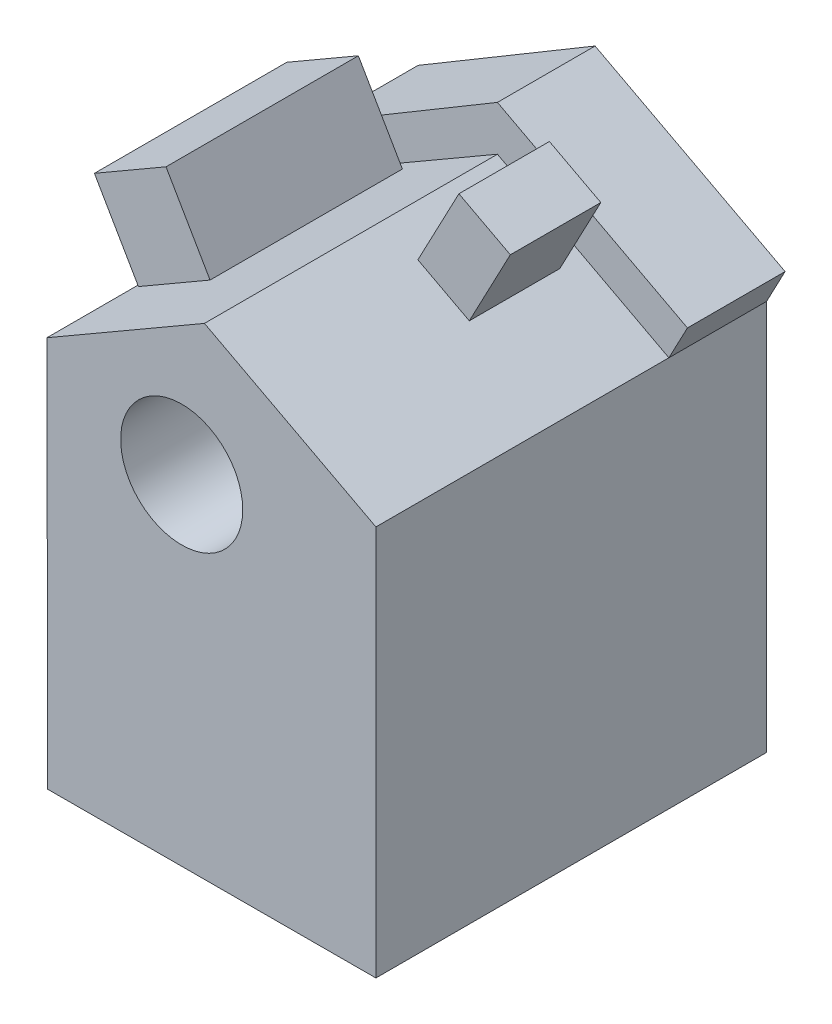
SolidWorks part; units mm, degrees
ref_plane "Front Plane" through (0, 0, 0) normal (0, 0, 1) x (1, 0, 0)
ref_plane "Top Plane" through (0, 0, 0) normal (0, 1, 0) x (1, 0, 0)
ref_plane "Right Plane" through (0, 0, 0) normal (1, 0, 0) x (0, 0, -1)
sketch "Sketch4" plane through (0, 0, 0) normal (0, 0, 1) x (1, 0, 0)
  line L0 (0, 0) -> (33.61, 0.0671)
  line L1 (0, 0) -> (-0.0798, 40)
  line L2 (-0.0798, 40) -> (16.0514, 49.3374)
  line L3 (16.0514, 49.3374) -> (33.61, 40.0671)
  line L4 (33.61, 40.0671) -> (33.61, 0.0671)
  dimension "D1" = 33.61
  dimension "D2" = 40
  dimension "D3" = 40
extrude "Boss-Extrude1" add sketch "Sketch4" along normal blind 40
sketch "Sketch5" plane through (0, 0, 40) normal (0, 0, 1) x (1, 0, 0)
  line L0 (0, 0) -> (33.61, 0.0671) construction
  line L6 (1.3588, 15.0227) -> (11.3588, 15.0227)
  line L7 (1.3588, 15.0227) -> (1.3588, 0.0227)
  line L9 (11.3588, 15.0227) -> (11.3588, 0.0227)
  circle A0 centre (13.7229, 34.7699) radius 6.25
  dimension "D3" = 12.5
  dimension "D1" = 15
  dimension "D2" = 10
extrude "Cut-Extrude6" cut sketch "Sketch5" against normal blind 10 contours A0
sketch "Sketch6" plane through (0, 0, 40) normal (0, 0, 1) x (1, 0, 0)
  line L0 (0, 0) -> (33.61, 0.0671) construction
  line L1 (5.2174, 15.0304) -> (15.2174, 15.0304)
  line L2 (5.2174, 15.0304) -> (5.2174, 0.0304)
  line L3 (5.2174, 0.0304) -> (15.2174, 0.0304)
  line L4 (15.2174, 15.0304) -> (15.2174, 0.0304)
  dimension "D1" = 15
  dimension "D2" = 10
sketch "Sketch7" plane through (0, 0, 0) normal (0, 0, 1) x (1, 0, 0)
  line L0 (16.0514, 49.3374) -> (33.61, 40.0671)
  line L1 (33.61, 40.0671) -> (35.5083, 43.6625)
  line L2 (35.5083, 43.6625) -> (16.0514, 53.935)
  line L3 (16.0514, 53.935) -> (-2.0715, 43.1572)
  line L4 (-2.0715, 43.1572) -> (-0.101, 39.8437)
  line L5 (-0.101, 39.8437) -> (-0.0796, 39.8564)
  line L6 (-0.0798, 40) -> (0, 0) construction
  line L12 (-0.0798, 40) -> (0, 0)
  line L13 (0, 0) -> (33.61, 0.0671)
  line L14 (33.61, 0.0671) -> (33.61, 40.0671)
  line L15 (33.61, 40.0671) -> (16.0514, 49.3374)
  line L16 (16.0514, 49.3374) -> (-0.0798, 40)
  line L17 (-0.0798, 40) -> (-0.0796, 39.8564)
  line L21 (16.0514, 49.3374) -> (-0.0798, 40)
  point P4 (12.5308, 54.4027)
  point P12 (16.0514, 53.935)
  dimension "D1" = 0
extrude "Boss-Extrude2" add sketch "Sketch7" along normal blind 10
sketch "Sketch8" plane through (23.8692, 45.2099, 0) normal (0.4669, 0.8843, 0) x (0.8843, -0.4669, 0)
  line L1 (-4.9257, -12.3402) -> (1.0271, -12.3402)
  line L2 (-4.9257, -12.3402) -> (-4.9257, -21.6063)
  line L3 (-4.9257, -21.6063) -> (1.0271, -21.6063)
  line L4 (1.0271, -12.3402) -> (1.0271, -21.6063)
  line L5 (-4.9257, -12.3402) -> (1.0271, -21.6063) construction
  line L6 (-4.9257, -21.6063) -> (1.0271, -12.3402) construction
  point P0 (-1.9493, -16.9733)
extrude "Boss-Extrude3" add sketch "Sketch8" along normal blind 9
sketch "Sketch9" plane through (-17.3628, 29.996, 0) normal (-0.501, 0.8655, 0) x (0.8655, 0.501, 0)
  line L1 (20.3861, -11.2911) -> (28.8571, -11.2911)
  line L2 (20.3861, -11.2911) -> (20.3861, -30.9864)
  line L3 (20.3861, -30.9864) -> (28.8571, -30.9864)
  line L4 (28.8571, -11.2911) -> (28.8571, -30.9864)
  line L5 (20.3861, -11.2911) -> (28.8571, -30.9864) construction
  line L6 (20.3861, -30.9864) -> (28.8571, -11.2911) construction
  point P0 (24.6216, -21.1387)
extrude "Boss-Extrude4" add sketch "Sketch9" along normal blind 9
sketch "Sketch11" plane through (0, 0, 10) normal (0, 0, 1) x (1, 0, 0)
  line L0 (16.0514, 53.935) -> (16.0514, 49.3374)
  line L1 (16.0514, 53.935) -> (-2.0715, 43.1572)
  line L2 (-2.0715, 43.1572) -> (-0.101, 39.8437)
  line L3 (-2.0715, 43.1572) -> (-0.101, 39.8437) construction
  line L4 (16.0514, 53.935) -> (35.5083, 43.6625)
  line L5 (16.0514, 49.3374) -> (16.0514, 51.6362)
  line L6 (16.0514, 51.6362) -> (34.5591, 41.8648)
  line L7 (33.61, 40.0671) -> (35.5083, 43.6625) construction
  line L8 (34.5591, 41.8648) -> (33.61, 40.0671)
  line L9 (16.0514, 51.6362) -> (-1.0862, 41.5004)
  line L10 (-1.0862, 41.5004) -> (-0.101, 39.8437)
